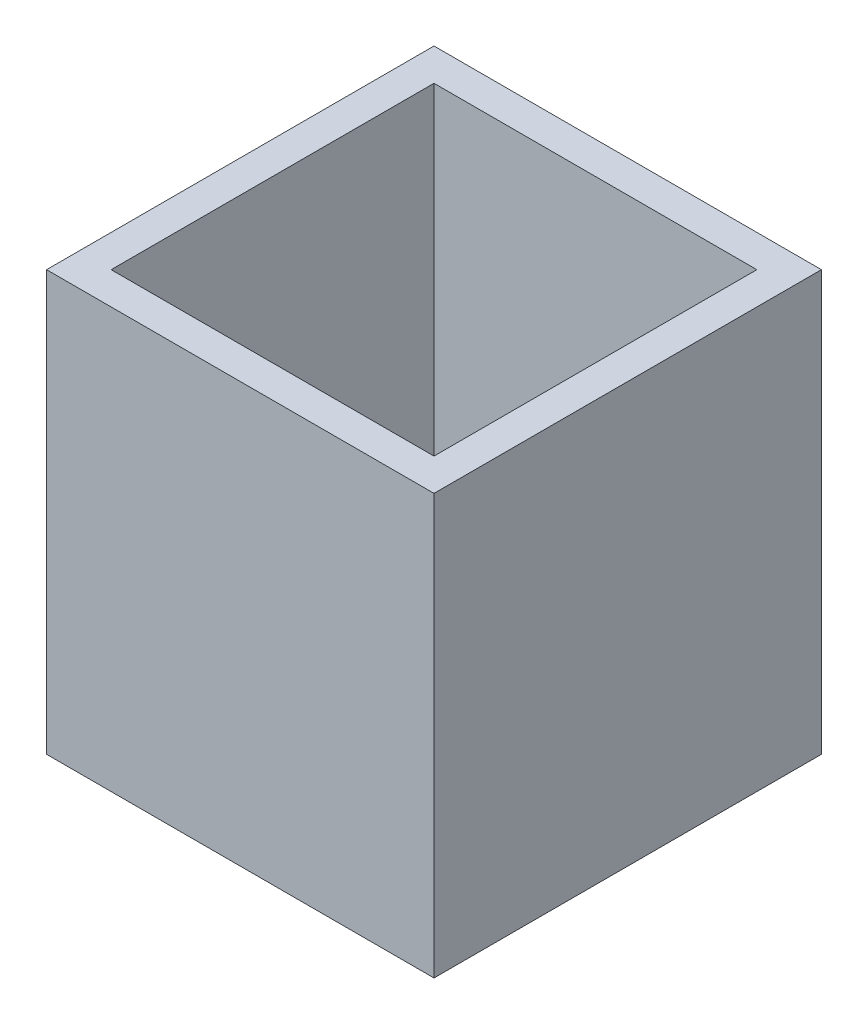
SolidWorks part; units mm, degrees
ref_plane "Front Plane" through (0, 0, 0) normal (0, 0, 1) x (1, 0, 0)
ref_plane "Top Plane" through (0, 0, 0) normal (0, 1, 0) x (1, 0, 0)
ref_plane "Right Plane" through (0, 0, 0) normal (1, 0, 0) x (0, 0, -1)
sketch "Sketch1" plane through (0, 0, 0) normal (0, 1, 0) x (1, 0, 0)
  line L1 (-25, -25) -> (25, -25)
  line L2 (-25, -25) -> (-25, 25)
  line L3 (-25, 25) -> (25, 25)
  line L4 (25, -25) -> (25, 25)
  line L5 (-25, -25) -> (25, 25) construction
  line L6 (-25, 25) -> (25, -25) construction
  line L7 (-30, -30) -> (30, -30)
  line L8 (-30, -30) -> (-30, 30)
  line L9 (-30, 30) -> (30, 30)
  line L10 (30, -30) -> (30, 30)
  line L11 (-30, -30) -> (30, 30) construction
  line L12 (-30, 30) -> (30, -30) construction
  point P0 (0, 0)
  point P6 (0, 0)
  dimension "D1" = 50
  dimension "D2" = 50
  dimension "D3" = 5
  dimension "D4" = 5
extrude "Boss-Extrude1" add sketch "Sketch1" along normal blind 60
sketch "Sketch2" plane through (0, 0, 0) normal (0, -1, 0) x (1, 0, 0)
  line L1 (-30, -30) -> (30, -30)
  line L2 (-30, -30) -> (-30, 30)
  line L3 (-30, 30) -> (30, 30)
  line L4 (30, -30) -> (30, 30)
  line L5 (-30, -30) -> (30, 30) construction
  line L6 (-30, 30) -> (30, -30) construction
  point P0 (0, 0)
extrude "Boss-Extrude2" add sketch "Sketch2" along normal blind 5
sketch "Sketch3" plane through (0, 0, -30) normal (0, 0, -1) x (-1, 0, 0)
  line L0 (-25, 0) -> (25, 0) construction
  line L1 (-25, 60) -> (-25, 0) construction
  circle A0 centre (0, 2.5) radius 1.25
  circle A1 centre (0, 8.1) radius 1.25
  dimension "D1" = 2.5
  dimension "D5" = 2.5
  dimension "D2" = 2.5
  dimension "D3" = 25
  dimension "D4" = 5.6
extrude "Cut-Extrude1" cut sketch "Sketch3" against normal up to surface (5 mm away) up to face at (0, 30, -25)
sketch "Sketch4" plane through (0, 0, -30) normal (0, 0, -1) x (-1, 0, 0)
  line L0 (0, 8.1) -> (-15.9728, 8.1) construction
  circle A0 centre (-13.1765, 8.1) radius 1.25
  dimension "D1" = 2.5
extrude "Cut-Extrude2" cut sketch "Sketch4" against normal up to next
